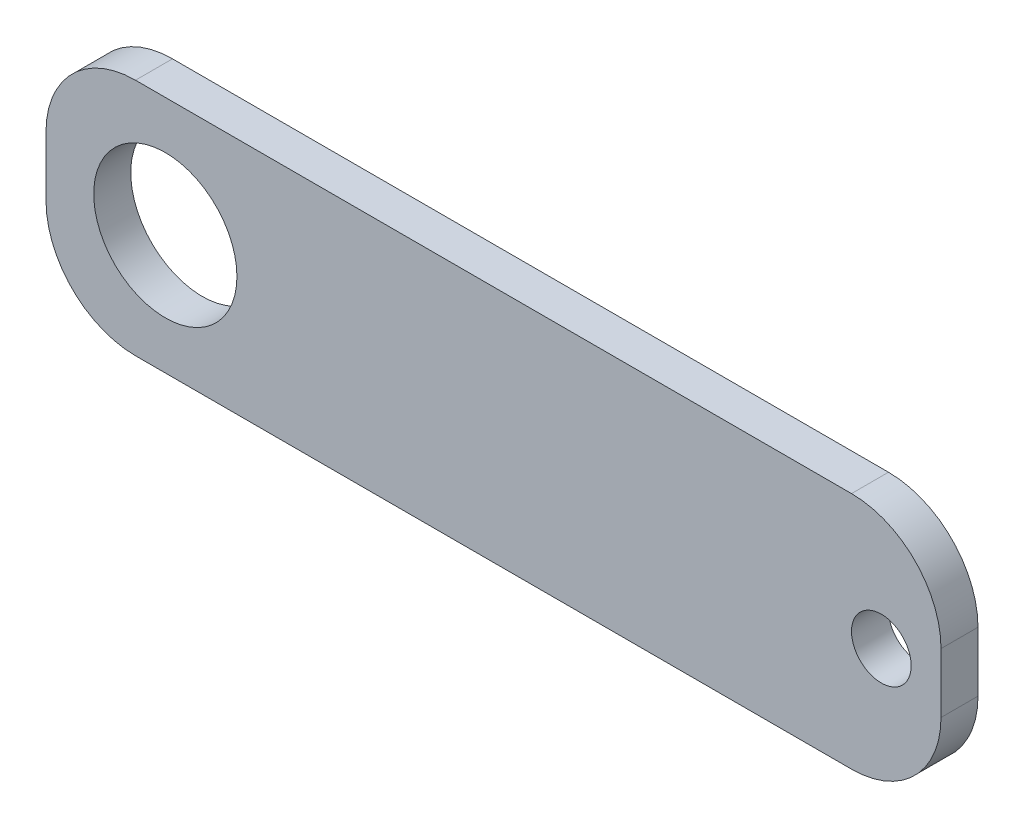
SolidWorks part; units mm, degrees
material "Teak"
ref_plane "Front Plane" through (0, 0, 0) normal (0, 0, 1) x (1, 0, 0)
ref_plane "Top Plane" through (0, 0, 0) normal (0, 1, 0) x (1, 0, 0)
ref_plane "Right Plane" through (0, 0, 0) normal (1, 0, 0) x (0, 0, -1)
sketch "Sketch1" plane through (0, 0, 0) normal (0, 0, 1) x (1, 0, 0)
  line L0 (-27.6194, -10) -> (47.3806, -10)
  line L1 (-27.6194, -10) -> (-27.6194, 10)
  line L2 (47.3806, -10) -> (47.3806, 10)
  line L3 (-27.6194, 10) -> (47.3806, 10)
  line L4 (-27.6194, -10) -> (47.3806, 10) construction
  line L5 (47.3806, -10) -> (-27.6194, 10) construction
  line L6 (-27.6194, 0) -> (47.3806, 0) construction
  line L7 (9.8806, 10) -> (9.8806, -10) construction
  line L8 (-17.6194, 0) -> (-17.6194, 10) construction
  circle A1 centre (42.3806, 0) radius 2.5
  circle A4 centre (-17.6194, 0) radius 6
  dimension "D3" = 12
  dimension "D8" = 60
  dimension "D1" = 5
  dimension "D2" = 20
  dimension "D4" = 10
  dimension "D7" = 5
extrude "Boss-Extrude1" add sketch "Sketch1" along normal blind 3.1
fillet "Fillet1" radius 7.5 4 edges at (-27.6194, -10, 1.55) (-27.6194, 10, 1.55) (47.3806, -10, 1.55) (47.3806, 10, 1.55)
equation "\"D1@Boss-Extrude1\"=\"thick\""
equation "\"p\"= 20mm"
equation "\"m\"= 1"
equation "\"hole_diam\"= 4mm"
equation "\"len_grip_1\" = 50mm"
equation "\"len_grip_2\" = 50mm"
equation "\"thick\" = 3.1mm"
equation "\"thick2\" = 20mm"
equation "\"wrist_cont_bearing_diam\"=3in"
equation "\"wrist_cont_bearing_thick\"=5/16in"
equation "\"len_forearm\" = 300mm"
equation "\"wrist_bearing_diam\"=3in"
equation "\"len_link\" = 7cm"
equation "\"D1@Sketch1\"=5mm"
equation "\"elbow_cont_bearing_diam\"=10cm"
equation "\"elbow_cont_bearing2_diam\"=7.5cm"
equation "\"small_bearing_outer\"=13mm"
equation "\"servo1_L\"=40.7mm"
equation "\"servo1_W\"=20.5mm"
equation "\"servo1_H\"=43.5mm"
equation "\"servo1_hL\"=49mm"
equation "\"servo1_hW\"=10mm"
equation "\"D7@Sketch1\"=\"D1@Sketch1\""
